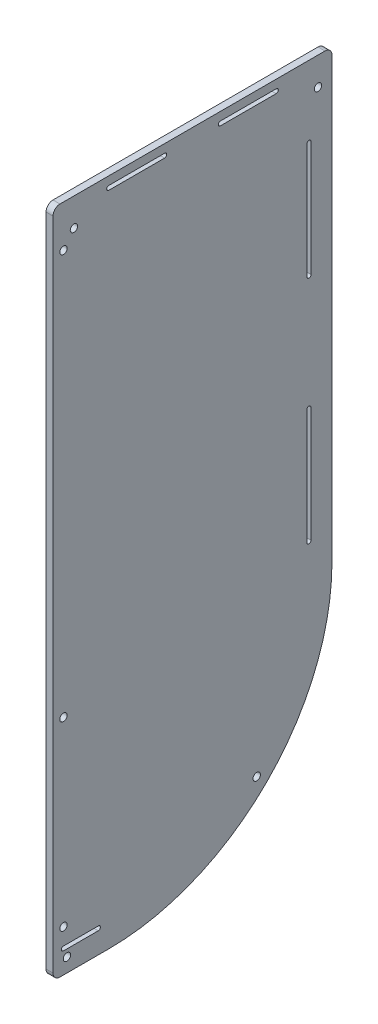
SolidWorks part; units mm, degrees
material "PC High Viscosity"
ref_plane "Front Plane" through (0, 0, 0) normal (0, 0, 1) x (1, 0, 0)
ref_plane "Top Plane" through (0, 0, 0) normal (0, 1, 0) x (1, 0, 0)
ref_plane "Right Plane" through (0, 0, 0) normal (1, 0, 0) x (0, 0, -1)
sketch "Sketch1" plane through (0, 0, 0) normal (1, 0, 0) x (0, 0, -1)
  line L0 (0, 0) -> (0, -609.6)
  line L1 (0, -609.6) -> (50.8, -609.6)
  line L2 (254, -406.4) -> (254, 0)
  line L3 (0, 0) -> (254, 0)
  arc A0 (50.8, -609.6) -> (254, -406.4) centre (50.8, -406.4) ccw
  dimension "D1" = 254
  dimension "D2" = 203.2
  dimension "D3" = 609.6
extrude "Boss-Extrude1" add sketch "Sketch1" along normal blind 6.35
sketch "Sketch2" plane through (6.35, 0, 0) normal (1, 0, 0) x (0, 0, -1)
  line L0 (254, 0) -> (0, 0) construction
  line L1 (254, -406.4) -> (254, 0) construction
  line L2 (50.8, -406.4) -> (185.5038, -541.1038) construction
  line L3 (0, 0) -> (0, -609.6) construction
  line L4 (0, -609.6) -> (50.8, -609.6) construction
  circle A0 centre (241.3, -25.4) radius 3.3655
  circle A2 centre (12.7, -596.9) radius 3.3655
  circle A3 centre (185.5038, -541.1038) radius 3.3655
  circle A4 centre (19.05, -25.4) radius 3.3655
  circle A6 centre (50.8, -406.4) radius 190.5 construction
  arc A7 (50.8, -609.6) -> (254, -406.4) centre (50.8, -406.4) ccw construction
  dimension "D1" = 25.4
  dimension "D3" = 6.731
  dimension "D4" = 381
  dimension "D8" = 222.25
  dimension "D2" = 12.7
  dimension "D5" = 45
  dimension "D6" = 12.7
  dimension "D7" = 12.7
extrude "Cut-Extrude1" cut sketch "Sketch2" against normal through all
fillet "Fillet1" radius 6.35 3 edges at (3.175, -609.6, 0) (3.175, 0, -254) (3.175, 0, 0)
sketch "Sketch3" plane through (6.35, 0, 0) normal (1, 0, 0) x (0, 0, -1)
  line L2 (50.8, -9.525) -> (101.6, -9.525) construction
  line L3 (50.8, -7.62) -> (101.6, -7.62)
  line L4 (50.8, -11.43) -> (101.6, -11.43)
  line L5 (152.4, -9.525) -> (203.2, -9.525) construction
  line L6 (152.4, -7.62) -> (203.2, -7.62)
  line L7 (152.4, -11.43) -> (203.2, -11.43)
  line L8 (0, -6.35) -> (0, -603.25) construction
  line L9 (247.65, 0) -> (6.35, 0) construction
  arc A2 (50.8, -7.62) -> (50.8, -11.43) centre (50.8, -9.525) ccw
  arc A3 (101.6, -11.43) -> (101.6, -7.62) centre (101.6, -9.525) ccw
  arc A4 (152.4, -7.62) -> (152.4, -11.43) centre (152.4, -9.525) ccw
  arc A5 (203.2, -11.43) -> (203.2, -7.62) centre (203.2, -9.525) ccw
  point P2 (76.2, -9.525)
  point P8 (177.8, -9.525)
  dimension "D1" = 50.8
  dimension "D4" = 9.525
  dimension "D2" = 76.2
  dimension "D3" = 101.6
  dimension "D5" = 3.81
extrude "Cut-Extrude6" cut sketch "Sketch3" against normal through all
sketch "Sketch4" plane through (6.35, 0, 0) normal (1, 0, 0) x (0, 0, -1)
  line L0 (247.65, 0) -> (6.35, 0) construction
  line L1 (6.35, -609.6) -> (50.8, -609.6) construction
  line L2 (0, -6.35) -> (0, -603.25) construction
  circle A0 centre (9.525, -38.1) radius 3.3655
  circle A1 centre (9.525, -406.4) radius 3.3655
  circle A2 centre (9.525, -571.5) radius 3.3655
  dimension "D1" = 6.731
  dimension "D2" = 38.1
  dimension "D3" = 38.1
  dimension "D4" = 165.1
  dimension "D5" = 9.525
extrude "Cut-Extrude3" cut sketch "Sketch4" against normal through all
sketch "Sketch6" plane through (6.35, 0, 0) normal (1, 0, 0) x (0, 0, -1)
  line L0 (233.045, -65.0875) -> (233.045, -169.8625) construction
  line L1 (234.95, -65.0875) -> (234.95, -169.8625)
  line L2 (231.14, -65.0875) -> (231.14, -169.8625)
  line L3 (254, -406.4) -> (254, -6.35) construction
  line L4 (247.65, 0) -> (6.35, 0) construction
  line L5 (233.045, -379.4125) -> (233.045, -274.6375) construction
  line L6 (231.14, -379.4125) -> (231.14, -274.6375)
  line L7 (234.95, -379.4125) -> (234.95, -274.6375)
  arc A0 (234.95, -65.0875) -> (231.14, -65.0875) centre (233.045, -65.0875) ccw
  arc A1 (231.14, -169.8625) -> (234.95, -169.8625) centre (233.045, -169.8625) ccw
  arc A2 (231.14, -379.4125) -> (234.95, -379.4125) centre (233.045, -379.4125) ccw
  arc A3 (234.95, -274.6375) -> (231.14, -274.6375) centre (233.045, -274.6375) ccw
  point P2 (233.045, -117.475)
  point P13 (233.045, -327.025)
  dimension "D1" = 3.81
  dimension "D2" = 19.05
  dimension "D3" = 104.775
  dimension "D4" = 117.475
  dimension "D5" = 327.025
extrude "Cut-Extrude7" cut sketch "Sketch6" against normal through all
sketch "Sketch7" plane through (6.35, 0, 0) normal (1, 0, 0) x (0, 0, -1)
  line L0 (9.525, -588.645) -> (41.275, -588.645) construction
  line L1 (9.525, -586.74) -> (41.275, -586.74)
  line L2 (9.525, -590.55) -> (41.275, -590.55)
  line L3 (6.35, -609.6) -> (50.8, -609.6) construction
  line L4 (0, -6.35) -> (0, -603.25) construction
  arc A0 (9.525, -586.74) -> (9.525, -590.55) centre (9.525, -588.645) ccw
  arc A1 (41.275, -590.55) -> (41.275, -586.74) centre (41.275, -588.645) ccw
  point P2 (25.4, -588.645)
  dimension "D1" = 19.05
  dimension "D2" = 3.81
  dimension "D3" = 25.4
  dimension "D4" = 31.75
extrude "Cut-Extrude8" cut sketch "Sketch7" against normal through all and the other way through all
